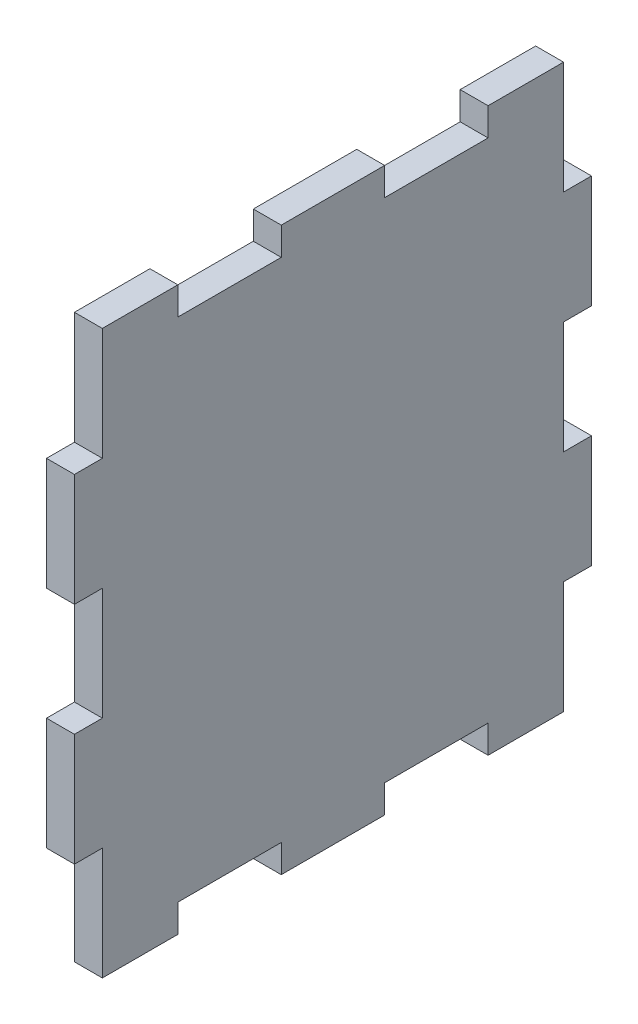
SolidWorks part; units mm, degrees
ref_plane "Ön Düzlem" through (0, 0, 0) normal (0, 0, 1) x (1, 0, 0)
ref_plane "Üst Düzlem" through (0, 0, 0) normal (0, 1, 0) x (1, 0, 0)
ref_plane "Sağ Düzlem" through (0, 0, 0) normal (1, 0, 0) x (0, 0, -1)
sketch "Sketch1" plane through (0, 0, 0) normal (1, 0, 0) x (0, 0, -1)
  line L0 (25, 5.44) -> (25, 16.32)
  line L1 (22.3, -27.2) -> (15, -27.2)
  line L3 (22.3, 27.2) -> (15, 27.2)
  line L8 (25, -16.32) -> (25, -5.44)
  line L9 (-22.3, 27.2) -> (-22.3, 16.32)
  line L10 (15, -24.5) -> (5, -24.5)
  line L11 (22.3, 27.2) -> (22.3, 16.32)
  line L12 (-5, -24.5) -> (-15, -24.5)
  line L14 (-25, -16.32) -> (-25, -5.44)
  line L16 (-25, 5.44) -> (-25, 16.32)
  line L19 (5, -27.2) -> (-5, -27.2)
  line L21 (-15, -27.2) -> (-22.3, -27.2)
  line L22 (-25, -16.32) -> (-22.3, -16.32)
  line L23 (-25, -5.44) -> (-22.3, -5.44)
  line L24 (-25, 5.44) -> (-22.3, 5.44)
  line L25 (-25, 16.32) -> (-22.3, 16.32)
  line L26 (22.3, -16.32) -> (25, -16.32)
  line L28 (22.3, -5.44) -> (25, -5.44)
  line L29 (15, -27.2) -> (15, -24.5)
  line L30 (22.3, 5.44) -> (25, 5.44)
  line L31 (5, -27.2) -> (5, -24.5)
  line L33 (-5, -27.2) -> (-5, -24.5)
  line L34 (22.3, 16.32) -> (25, 16.32)
  line L35 (-15, -27.2) -> (-15, -24.5)
  line L36 (-15, 24.5) -> (-15, 27.2)
  line L38 (-22.3, -16.32) -> (-22.3, -27.2)
  line L39 (-22.3, 5.44) -> (-22.3, -5.44)
  line L40 (-5, 24.5) -> (-5, 27.2)
  line L41 (5, 24.5) -> (5, 27.2)
  line L42 (15, 24.5) -> (15, 27.2)
  line L43 (-15, 27.2) -> (-22.3, 27.2)
  line L44 (5, 27.2) -> (-5, 27.2)
  line L45 (-15, 24.5) -> (-5, 24.5)
  line L46 (5, 24.5) -> (15, 24.5)
  line L48 (22.3, 5.44) -> (22.3, -5.44)
  line L49 (22.3, -16.32) -> (22.3, -27.2)
  point P0 (0, 0)
extrude "Boss-Extrude1" add sketch "Sketch1" along normal blind 2.7
